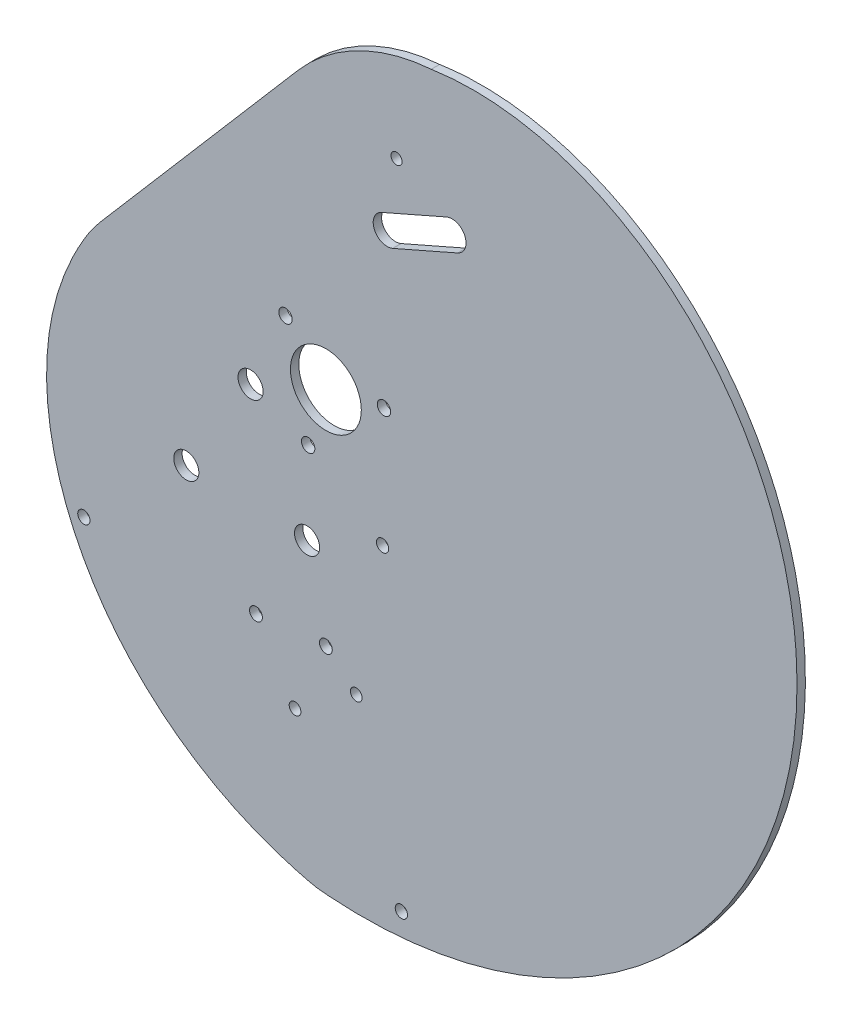
SolidWorks part; units mm, degrees
ref_plane "Front Plane" through (0, 0, 0) normal (0, 0, 1) x (1, 0, 0)
ref_plane "Top Plane" through (0, 0, 0) normal (0, 1, 0) x (1, 0, 0)
ref_plane "Right Plane" through (0, 0, 0) normal (1, 0, 0) x (0, 0, -1)
curve "Curve1"
sketch "Sketch1" plane through (0, 0, 0) normal (0, 0, 1) x (1, 0, 0)
  line L0 (10.9805, 30.1851) -> (22.6104, 35.2876) construction
  line L1 (9.976, 32.4744) -> (21.6059, 37.5769)
  line L2 (11.9849, 27.8957) -> (23.6148, 32.9983)
  line L3 (10.7688, 46.4724) -> (16.7954, 32.7363) construction
  line L4 (-15.5247, -36.542) -> (-17.0714, -47.8252) construction
  line L5 (-12.072, -37.0153) -> (-13.6188, -48.2986) construction
  line L6 (-18.9773, -36.0687) -> (-20.5241, -47.3519) construction
  line L7 (-15.1851, -34.0651) -> (-15.8642, -39.0188) construction
  line L8 (5.6152, 38.2953) -> (3.8561, 42.4197)
  line L9 (20.342, 44.5764) -> (18.4912, 48.9157)
  circle A0 centre (0, 0) radius 6.35
  arc A1 (9.976, 32.4744) -> (11.9849, 27.8957) centre (10.9805, 30.1851) ccw
  arc A2 (23.6148, 32.9983) -> (21.6059, 37.5769) centre (22.6104, 35.2876) ccw
  arc A3 (5.6152, 38.2953) -> (20.342, 44.5764) centre (12.9786, 41.4359) ccw
  arc A4 (-12.072, -37.0153) -> (-18.9773, -36.0687) centre (-15.5247, -36.542) ccw construction
  arc A5 (-20.5241, -47.3519) -> (-13.6188, -48.2986) centre (-17.0714, -47.8252) ccw construction
  spline S0 degree 3 poles (-1.1843, -67.9504) (-0.014, -68.2767) (1.195, -68.3213) (2.3889, -68.4148) (3.5889, -68.4701) (4.791, -68.5105) (5.9959, -68.5295) (7.203, -68.5287) (8.412, -68.5074) (9.6226, -68.4657) (10.8344, -68.4032) (12.047, -68.32) (13.2602, -68.2159) (14.4735, -68.0908) (15.6866, -67.9446) (16.8991, -67.777) (18.1106, -67.5882) (19.3207, -67.3779) (20.529, -67.1461) (21.7351, -66.8927) (22.9386, -66.6176) (24.1392, -66.3208) (25.3362, -66.0022) (26.5295, -65.6619) (27.7184, -65.2996) (28.9026, -64.9155) (30.0816, -64.5096) (31.2551, -64.0817) (32.4225, -63.632) (33.5833, -63.1604) (34.7372, -62.667) (35.8837, -62.1518) (37.0223, -61.6149) (38.1525, -61.0563) (39.2739, -60.4761) (40.3861, -59.8743) (41.4885, -59.2512) (42.5806, -58.6068) (43.6621, -57.9411) (44.7324, -57.2544) (45.791, -56.5468) (46.8375, -55.8184) (47.8714, -55.0695) (48.8923, -54.3001) (49.8996, -53.5105) (50.8929, -52.7009) (51.8717, -51.8715) (52.8356, -51.0225) (53.7841, -50.1542) (54.7166, -49.2668) (55.6329, -48.3607) (56.5323, -47.436) (57.4145, -46.4932) (58.279, -45.5324) (59.1254, -44.554) (59.9531, -43.5583) (60.7619, -42.5458) (61.5512, -41.5167) (62.3207, -40.4714) (63.0698, -39.4103) (63.7983, -38.3338) (64.5057, -37.2423) (65.1916, -36.1362) (65.8556, -35.016) (66.4973, -33.882) (67.1165, -32.7348) (67.7126, -31.5748) (68.2854, -30.4026) (68.8345, -29.2185) (69.3596, -28.023) (69.8603, -26.8168) (70.3364, -25.6003) (70.7876, -24.3741) (71.2134, -23.1386) (71.6138, -21.8945) (71.9884, -20.6423) (72.337, -19.3826) (72.6592, -18.116) (72.955, -16.843) (73.224, -15.5643) (73.4661, -14.2804) (73.6812, -12.992) (73.8689, -11.6997) (74.0292, -10.4042) (74.1619, -9.106) (74.2669, -7.8058) (74.3441, -6.5043) (74.3933, -5.2021) (74.4146, -3.9) (74.4078, -2.5984) (74.3729, -1.2982) (74.3098, -0.0001) (74.2186, 1.2954) (74.0993, 2.5875) (73.9518, 3.8756) (73.7762, 5.1589) (73.5725, 6.4367) (73.3409, 7.7084) (73.0814, 8.9732) (72.7942, 10.2305) (72.4792, 11.4795) (72.1368, 12.7196) (71.767, 13.95) (71.3701, 15.1701) (70.9462, 16.3792) (70.4955, 17.5765) (70.0184, 18.7613) (69.515, 19.9331) (68.9856, 21.091) (68.4305, 22.2344) (67.85, 23.3626) (67.2445, 24.475) (66.6143, 25.5709) (65.9598, 26.6495) (65.2813, 27.7103) (64.5793, 28.7526) (63.8542, 29.7758) (63.1064, 30.7792) (62.3364, 31.7621) (61.5447, 32.7241) (60.7318, 33.6643) (59.8981, 34.5824) (59.0442, 35.4776) (58.1707, 36.3494) (57.2782, 37.1972) (56.3671, 38.0204) (55.4383, 38.8186) (54.4923, 39.5913) (53.53, 40.3381) (52.552, 41.0585) (51.5591, 41.7521) (50.552, 42.4186) (49.5315, 43.0576) (48.4984, 43.6687) (47.4535, 44.2516) (46.3974, 44.8061) (45.3311, 45.3318) (44.2553, 45.8284) (43.1709, 46.2958) (42.0786, 46.7338) (40.9793, 47.1421) (39.8737, 47.5205) (38.7628, 47.869) (37.6473, 48.1874) (36.5281, 48.4755) (35.4061, 48.7334) (34.282, 48.961) (33.1567, 49.1581) (32.031, 49.3249) (30.9059, 49.4613) (29.7821, 49.5673) (28.6604, 49.6431) (27.5418, 49.6886) (26.427, 49.7041) (25.3169, 49.6895) (24.2124, 49.6451) (23.1141, 49.571) (22.0231, 49.4674) (20.94, 49.3346) (19.8657, 49.1727) (18.801, 48.982) (17.7468, 48.7628) (16.7037, 48.5154) (15.6726, 48.2401) (14.6543, 47.9373) (13.6495, 47.6073) (12.659, 47.2504) (11.6836, 46.8672) (10.7239, 46.458) (9.7807, 46.0233) (8.8547, 45.5635) (7.9467, 45.0791) (7.0573, 44.5706) (6.1871, 44.0386) (5.3369, 43.4835) (4.5074, 42.906) (3.699, 42.3065) (2.9126, 41.6858) (2.1491, 41.0448) (1.4087, 40.3857) (0.692, 39.711) (-0.0007, 39.0233) (-0.6692, 38.3252) (-1.3135, 37.6192) (-1.9336, 36.908) (-2.5298, 36.194) (-3.1024, 35.4799) (-3.6521, 34.7682) (-4.1795, 34.0612) (-4.6854, 33.3616) (-5.1709, 32.6716) (-5.637, 31.9937) (-6.085, 31.3301) (-6.5163, 30.6831) (-6.9325, 30.0548) (-7.3352, 29.4474) (-7.7263, 28.8629) (-8.1078, 28.3032) (-8.4816, 27.77) (-8.8501, 27.2652) (-9.216, 26.7897) (-9.5801, 26.3424) (-9.9432, 25.9213) (-10.3062, 25.5243) (-10.6698, 25.1494) (-11.0346, 24.7946) (-11.4009, 24.4578) (-11.7691, 24.1369) (-12.1394, 23.8299) (-12.5117, 23.5348) (-12.8861, 23.2497) (-13.2622, 22.9725) (-13.6397, 22.7014) (-14.0182, 22.4345) (-14.3971, 22.1699) (-14.7757, 21.906) (-15.1531, 21.6409) (-15.5285, 21.3732) (-15.9009, 21.1012) (-16.269, 20.8234) (-16.6317, 20.5384) (-16.9875, 20.2449) (-17.3351, 19.9417) (-17.6745, 19.6295) (-18.0059, 19.3089) (-18.3295, 18.9807) (-18.6455, 18.6455) (-18.9542, 18.3039) (-19.2559, 17.9565) (-19.5509, 17.6038) (-19.8396, 17.2464) (-20.1224, 16.8848) (-20.3997, 16.5195) (-20.672, 16.1508) (-20.9397, 15.7793) (-21.2033, 15.4052) (-21.4634, 15.0289) (-21.7205, 14.6507) (-21.9753, 14.2708) (-22.2281, 13.8895) (-22.4798, 13.507) (-22.7308, 13.1233) (-22.9819, 12.7386) (-23.2336, 12.3529) (-23.4866, 11.9663) (-23.7416, 11.5787) (-23.9993, 11.19) (-24.2602, 10.8001) (-24.5251, 10.4088) (-24.7947, 10.016) (-25.0696, 9.6214) (-25.3504, 9.2246) (-25.6379, 8.8254) (-25.9327, 8.4234) (-26.2354, 8.018) (-26.5467, 7.609) (-26.8672, 7.1956) (-27.1974, 6.7776) (-27.537, 6.3539) (-27.8856, 5.9238) (-28.2424, 5.4864) (-28.6069, 5.0408) (-28.9783, 4.5865) (-29.3562, 4.1226) (-29.7396, 3.6485) (-30.1278, 3.1637) (-30.5202, 2.6674) (-30.9158, 2.1592) (-31.314, 1.6386) (-31.7137, 1.1051) (-32.1143, 0.5583) (-32.5148, -0.0021) (-32.9143, -0.5765) (-33.3119, -1.1651) (-33.7067, -1.7682) (-34.0978, -2.3859) (-34.4843, -3.0184) (-34.8652, -3.6658) (-35.2396, -4.3281) (-35.6066, -5.0053) (-35.9651, -5.6973) (-36.3143, -6.404) (-36.6531, -7.1254) (-36.9808, -7.8611) (-37.2963, -8.611) (-37.5988, -9.3748) (-37.8873, -10.1521) (-38.1609, -10.9426) (-38.4187, -11.7459) (-38.66, -12.5613) (-38.8837, -13.3886) (-39.0892, -14.2271) (-39.2755, -15.0762) (-39.4422, -15.9354) (-39.589, -16.8043) (-39.7155, -17.6823) (-39.8215, -18.5689) (-39.9067, -19.4636) (-39.9709, -20.366) (-40.0137, -21.2755) (-40.035, -22.1916) (-40.0345, -23.1138) (-40.0119, -24.0415) (-39.9672, -24.9742) (-39.9002, -25.9114) (-39.8105, -26.8525) (-39.6982, -27.7969) (-39.563, -28.7442) (-39.4048, -29.6936) (-39.2235, -30.6448) (-39.019, -31.597) (-38.7911, -32.5497) (-38.5399, -33.5023) (-38.2653, -34.4543) (-37.9672, -35.4051) (-37.6456, -36.354) (-37.3004, -37.3005) (-36.9317, -38.2441) (-36.5395, -39.184) (-36.1238, -40.1197) (-35.6847, -41.0507) (-35.2221, -41.9763) (-34.7363, -42.896) (-34.2272, -43.8091) (-33.695, -44.715) (-33.1398, -45.6133) (-32.5617, -46.5032) (-31.9609, -47.3843) (-31.3375, -48.2559) (-30.6917, -49.1174) (-30.0238, -49.9683) (-29.3338, -50.808) (-28.6221, -51.636) (-27.8888, -52.4517) (-27.1343, -53.2545) (-26.3587, -54.0439) (-25.5624, -54.8193) (-24.7457, -55.5802) (-23.9088, -56.3261) (-23.0521, -57.0564) (-22.1759, -57.7707) (-21.2805, -58.4684) (-20.3664, -59.149) (-19.4339, -59.812) (-18.4833, -60.4569) (-17.5151, -61.0833) (-16.5298, -61.6908) (-15.5276, -62.2787) (-14.5091, -62.8467) (-13.4747, -63.3944) (-12.4248, -63.9213) (-11.36, -64.4271) (-10.2807, -64.9112) (-9.1874, -65.3733) (-8.0806, -65.8131) (-6.9608, -66.2301) (-5.8286, -66.6239) (-4.6845, -66.9947) (-3.5289, -67.3403) (-2.3631, -67.6669) (-1.1843, -67.9504) (-0.014, -68.2767) (1.195, -68.3213) knots -0.0101 -0.006743 -0.003377 0 0.00332 0.006645 0.009976 0.013312 0.016655 0.020003 0.023357 0.026716 0.030082 0.033453 0.036831 0.040214 0.043603 0.046998 0.050399 0.053806 0.057218 0.060637 0.064061 0.067491 0.070927 0.074369 0.077816 0.081269 0.084728 0.088192 0.091662 0.095138 0.098619 0.102105 0.105597 0.109094 0.112596 0.116103 0.119615 0.123133 0.126655 0.130182 0.133714 0.137251 0.140792 0.144337 0.147888 0.151442 0.155 0.158563 0.16213 0.1657 0.169275 0.172853 0.176434 0.180019 0.183607 0.187199 0.190793 0.19439 0.19799 0.201593 0.205199 0.208806 0.212416 0.216028 0.219642 0.223258 0.226875 0.230494 0.234115 0.237736 0.241359 0.244982 0.248606 0.252231 0.255856 0.259481 0.263106 0.266731 0.270356 0.273981 0.277605 0.281228 0.28485 0.28847 0.29209 0.295708 0.299324 0.302939 0.306551 0.310161 0.313769 0.317374 0.320976 0.324575 0.328171 0.331763 0.335352 0.338938 0.342519 0.346096 0.349669 0.353237 0.356801 0.360359 0.363913 0.367461 0.371004 0.374541 0.378073 0.381598 0.385117 0.38863 0.392136 0.395636 0.399128 0.402614 0.406092 0.409563 0.413026 0.416482 0.419929 0.423369 0.4268 0.430223 0.433637 0.437043 0.44044 0.443828 0.447206 0.450575 0.453935 0.457284 0.460624 0.463953 0.467272 0.47058 0.473877 0.477164 0.480439 0.483703 0.486955 0.490196 0.493426 0.496643 0.499848 0.503042 0.506223 0.509391 0.512547 0.515691 0.518822 0.52194 0.525045 0.528137 0.531216 0.534282 0.537335 0.540375 0.543401 0.546414 0.549414 0.5524 0.555374 0.558333 0.56128 0.564213 0.567133 0.57004 0.572933 0.575814 0.578681 0.581535 0.584377 0.587205 0.590021 0.592825 0.595616 0.598394 0.60116 0.603911 0.606642 0.60935 0.612032 0.614684 0.617303 0.619884 0.622424 0.62492 0.627367 0.629763 0.632104 0.634387 0.636609 0.638767 0.640858 0.64288 0.644831 0.64671 0.648517 0.65025 0.651911 0.653509 0.655048 0.656538 0.657984 0.659394 0.660772 0.662125 0.663458 0.664774 0.666078 0.667373 0.668662 0.669946 0.671227 0.672507 0.673786 0.675065 0.676344 0.677623 0.678903 0.680182 0.681461 0.68274 0.684019 0.685298 0.686575 0.687853 0.689129 0.690404 0.691679 0.692952 0.694224 0.695495 0.696765 0.698035 0.699304 0.700572 0.70184 0.703109 0.704379 0.705651 0.706925 0.708202 0.709483 0.71077 0.712063 0.713364 0.714674 0.715995 0.717328 0.718676 0.72004 0.721422 0.722825 0.72425 0.7257 0.727177 0.728683 0.730218 0.731784 0.73338 0.735008 0.736668 0.738359 0.740082 0.741837 0.743623 0.745441 0.747291 0.749171 0.751082 0.753022 0.754993 0.756992 0.759021 0.761077 0.76316 0.765271 0.767407 0.769569 0.771756 0.773967 0.776201 0.778458 0.780736 0.783036 0.785357 0.787697 0.790056 0.792433 0.794828 0.797239 0.799666 0.80211 0.804571 0.807047 0.80954 0.812049 0.814575 0.817116 0.819674 0.822248 0.824838 0.827444 0.830066 0.832704 0.835358 0.838027 0.840713 0.843414 0.846131 0.848864 0.851612 0.854376 0.857155 0.859949 0.862759 0.865584 0.868424 0.871279 0.874149 0.877033 0.879933 0.882847 0.885776 0.88872 0.891678 0.89465 0.897636 0.900637 0.903651 0.906679 0.909721 0.912777 0.915847 0.91893 0.922026 0.925135 0.928258 0.931393 0.934541 0.937702 0.940876 0.944062 0.947261 0.950471 0.953694 0.956929 0.960175 0.963433 0.966703 0.969984 0.973276 0.976579 0.979893 0.983218 0.986554 0.9899 0.993257 0.996623 1 1.00332 1.006645 1.009976 only from (0, -68.2309) to (0, -68.2309) construction
  spline S1 degree 3 poles (-1.1843, -67.9504) (-0.014, -68.2767) (1.195, -68.3213) (2.3889, -68.4148) (3.5889, -68.4701) (4.791, -68.5105) (5.9959, -68.5295) (7.203, -68.5287) (8.412, -68.5074) (9.6226, -68.4657) (10.8344, -68.4032) (12.047, -68.32) (13.2602, -68.2159) (14.4735, -68.0908) (15.6866, -67.9446) (16.8991, -67.777) (18.1106, -67.5882) (19.3207, -67.3779) (20.529, -67.1461) (21.7351, -66.8927) (22.9386, -66.6176) (24.1392, -66.3208) (25.3362, -66.0022) (26.5295, -65.6619) (27.7184, -65.2996) (28.9026, -64.9155) (30.0816, -64.5096) (31.2551, -64.0817) (32.4225, -63.632) (33.5833, -63.1604) (34.7372, -62.667) (35.8837, -62.1518) (37.0223, -61.6149) (38.1525, -61.0563) (39.2739, -60.4761) (40.3861, -59.8743) (41.4885, -59.2512) (42.5806, -58.6068) (43.6621, -57.9411) (44.7324, -57.2544) (45.791, -56.5468) (46.8375, -55.8184) (47.8714, -55.0695) (48.8923, -54.3001) (49.8996, -53.5105) (50.8929, -52.7009) (51.8717, -51.8715) (52.8356, -51.0225) (53.7841, -50.1542) (54.7166, -49.2668) (55.6329, -48.3607) (56.5323, -47.436) (57.4145, -46.4932) (58.279, -45.5324) (59.1254, -44.554) (59.9531, -43.5583) (60.7619, -42.5458) (61.5512, -41.5167) (62.3207, -40.4714) (63.0698, -39.4103) (63.7983, -38.3338) (64.5057, -37.2423) (65.1916, -36.1362) (65.8556, -35.016) (66.4973, -33.882) (67.1165, -32.7348) (67.7126, -31.5748) (68.2854, -30.4026) (68.8345, -29.2185) (69.3596, -28.023) (69.8603, -26.8168) (70.3364, -25.6003) (70.7876, -24.3741) (71.2134, -23.1386) (71.6138, -21.8945) (71.9884, -20.6423) (72.337, -19.3826) (72.6592, -18.116) (72.955, -16.843) (73.224, -15.5643) (73.4661, -14.2804) (73.6812, -12.992) (73.8689, -11.6997) (74.0292, -10.4042) (74.1619, -9.106) (74.2669, -7.8058) (74.3441, -6.5043) (74.3933, -5.2021) (74.4146, -3.9) (74.4078, -2.5984) (74.3729, -1.2982) (74.3098, -0.0001) (74.2186, 1.2954) (74.0993, 2.5875) (73.9518, 3.8756) (73.7762, 5.1589) (73.5725, 6.4367) (73.3409, 7.7084) (73.0814, 8.9732) (72.7942, 10.2305) (72.4792, 11.4795) (72.1368, 12.7196) (71.767, 13.95) (71.3701, 15.1701) (70.9462, 16.3792) (70.4955, 17.5765) (70.0184, 18.7613) (69.515, 19.9331) (68.9856, 21.091) (68.4305, 22.2344) (67.85, 23.3626) (67.2445, 24.475) (66.6143, 25.5709) (65.9598, 26.6495) (65.2813, 27.7103) (64.5793, 28.7526) (63.8542, 29.7758) (63.1064, 30.7792) (62.3364, 31.7621) (61.5447, 32.7241) (60.7318, 33.6643) (59.8981, 34.5824) (59.0442, 35.4776) (58.1707, 36.3494) (57.2782, 37.1972) (56.3671, 38.0204) (55.4383, 38.8186) (54.4923, 39.5913) (53.53, 40.3381) (52.552, 41.0585) (51.5591, 41.7521) (50.552, 42.4186) (49.5315, 43.0576) (48.4984, 43.6687) (47.4535, 44.2516) (46.3974, 44.8061) (45.3311, 45.3318) (44.2553, 45.8284) (43.1709, 46.2958) (42.0786, 46.7338) (40.9793, 47.1421) (39.8737, 47.5205) (38.7628, 47.869) (37.6473, 48.1874) (36.5281, 48.4755) (35.4061, 48.7334) (34.282, 48.961) (33.1567, 49.1581) (32.031, 49.3249) (30.9059, 49.4613) (29.7821, 49.5673) (28.6604, 49.6431) (27.5418, 49.6886) (26.427, 49.7041) (25.3169, 49.6895) (24.2124, 49.6451) (23.1141, 49.571) (22.0231, 49.4674) (20.94, 49.3346) (19.8657, 49.1727) (18.801, 48.982) (17.7468, 48.7628) (16.7037, 48.5154) (15.6726, 48.2401) (14.6543, 47.9373) (13.6495, 47.6073) (12.659, 47.2504) (11.6836, 46.8672) (10.7239, 46.458) (9.7807, 46.0233) (8.8547, 45.5635) (7.9467, 45.0791) (7.0573, 44.5706) (6.1871, 44.0386) (5.3369, 43.4835) (4.5074, 42.906) (3.699, 42.3065) (2.9126, 41.6858) (2.1491, 41.0448) (1.4087, 40.3857) (0.692, 39.711) (-0.0007, 39.0233) (-0.6692, 38.3252) (-1.3135, 37.6192) (-1.9336, 36.908) (-2.5298, 36.194) (-3.1024, 35.4799) (-3.6521, 34.7682) (-4.1795, 34.0612) (-4.6854, 33.3616) (-5.1709, 32.6716) (-5.637, 31.9937) (-6.085, 31.3301) (-6.5163, 30.6831) (-6.9325, 30.0548) (-7.3352, 29.4474) (-7.7263, 28.8629) (-8.1078, 28.3032) (-8.4816, 27.77) (-8.8501, 27.2652) (-9.216, 26.7897) (-9.5801, 26.3424) (-9.9432, 25.9213) (-10.3062, 25.5243) (-10.6698, 25.1494) (-11.0346, 24.7946) (-11.4009, 24.4578) (-11.7691, 24.1369) (-12.1394, 23.8299) (-12.5117, 23.5348) (-12.8861, 23.2497) (-13.2622, 22.9725) (-13.6397, 22.7014) (-14.0182, 22.4345) (-14.3971, 22.1699) (-14.7757, 21.906) (-15.1531, 21.6409) (-15.5285, 21.3732) (-15.9009, 21.1012) (-16.269, 20.8234) (-16.6317, 20.5384) (-16.9875, 20.2449) (-17.3351, 19.9417) (-17.6745, 19.6295) (-18.0059, 19.3089) (-18.3295, 18.9807) (-18.6455, 18.6455) (-18.9542, 18.3039) (-19.2559, 17.9565) (-19.5509, 17.6038) (-19.8396, 17.2464) (-20.1224, 16.8848) (-20.3997, 16.5195) (-20.672, 16.1508) (-20.9397, 15.7793) (-21.2033, 15.4052) (-21.4634, 15.0289) (-21.7205, 14.6507) (-21.9753, 14.2708) (-22.2281, 13.8895) (-22.4798, 13.507) (-22.7308, 13.1233) (-22.9819, 12.7386) (-23.2336, 12.3529) (-23.4866, 11.9663) (-23.7416, 11.5787) (-23.9993, 11.19) (-24.2602, 10.8001) (-24.5251, 10.4088) (-24.7947, 10.016) (-25.0696, 9.6214) (-25.3504, 9.2246) (-25.6379, 8.8254) (-25.9327, 8.4234) (-26.2354, 8.018) (-26.5467, 7.609) (-26.8672, 7.1956) (-27.1974, 6.7776) (-27.537, 6.3539) (-27.8856, 5.9238) (-28.2424, 5.4864) (-28.6069, 5.0408) (-28.9783, 4.5865) (-29.3562, 4.1226) (-29.7396, 3.6485) (-30.1278, 3.1637) (-30.5202, 2.6674) (-30.9158, 2.1592) (-31.314, 1.6386) (-31.7137, 1.1051) (-32.1143, 0.5583) (-32.5148, -0.0021) (-32.9143, -0.5765) (-33.3119, -1.1651) (-33.7067, -1.7682) (-34.0978, -2.3859) (-34.4843, -3.0184) (-34.8652, -3.6658) (-35.2396, -4.3281) (-35.6066, -5.0053) (-35.9651, -5.6973) (-36.3143, -6.404) (-36.6531, -7.1254) (-36.9808, -7.8611) (-37.2963, -8.611) (-37.5988, -9.3748) (-37.8873, -10.1521) (-38.1609, -10.9426) (-38.4187, -11.7459) (-38.66, -12.5613) (-38.8837, -13.3886) (-39.0892, -14.2271) (-39.2755, -15.0762) (-39.4422, -15.9354) (-39.589, -16.8043) (-39.7155, -17.6823) (-39.8215, -18.5689) (-39.9067, -19.4636) (-39.9709, -20.366) (-40.0137, -21.2755) (-40.035, -22.1916) (-40.0345, -23.1138) (-40.0119, -24.0415) (-39.9672, -24.9742) (-39.9002, -25.9114) (-39.8105, -26.8525) (-39.6982, -27.7969) (-39.563, -28.7442) (-39.4048, -29.6936) (-39.2235, -30.6448) (-39.019, -31.597) (-38.7911, -32.5497) (-38.5399, -33.5023) (-38.2653, -34.4543) (-37.9672, -35.4051) (-37.6456, -36.354) (-37.3004, -37.3005) (-36.9317, -38.2441) (-36.5395, -39.184) (-36.1238, -40.1197) (-35.6847, -41.0507) (-35.2221, -41.9763) (-34.7363, -42.896) (-34.2272, -43.8091) (-33.695, -44.715) (-33.1398, -45.6133) (-32.5617, -46.5032) (-31.9609, -47.3843) (-31.3375, -48.2559) (-30.6917, -49.1174) (-30.0238, -49.9683) (-29.3338, -50.808) (-28.6221, -51.636) (-27.8888, -52.4517) (-27.1343, -53.2545) (-26.3587, -54.0439) (-25.5624, -54.8193) (-24.7457, -55.5802) (-23.9088, -56.3261) (-23.0521, -57.0564) (-22.1759, -57.7707) (-21.2805, -58.4684) (-20.3664, -59.149) (-19.4339, -59.812) (-18.4833, -60.4569) (-17.5151, -61.0833) (-16.5298, -61.6908) (-15.5276, -62.2787) (-14.5091, -62.8467) (-13.4747, -63.3944) (-12.4248, -63.9213) (-11.36, -64.4271) (-10.2807, -64.9112) (-9.1874, -65.3733) (-8.0806, -65.8131) (-6.9608, -66.2301) (-5.8286, -66.6239) (-4.6845, -66.9947) (-3.5289, -67.3403) (-2.3631, -67.6669) (-1.1843, -67.9504) (-0.014, -68.2767) (1.195, -68.3213) knots -0.0101 -0.006743 -0.003377 0 0.00332 0.006645 0.009976 0.013312 0.016655 0.020003 0.023357 0.026716 0.030082 0.033453 0.036831 0.040214 0.043603 0.046998 0.050399 0.053806 0.057218 0.060637 0.064061 0.067491 0.070927 0.074369 0.077816 0.081269 0.084728 0.088192 0.091662 0.095138 0.098619 0.102105 0.105597 0.109094 0.112596 0.116103 0.119615 0.123133 0.126655 0.130182 0.133714 0.137251 0.140792 0.144337 0.147888 0.151442 0.155 0.158563 0.16213 0.1657 0.169275 0.172853 0.176434 0.180019 0.183607 0.187199 0.190793 0.19439 0.19799 0.201593 0.205199 0.208806 0.212416 0.216028 0.219642 0.223258 0.226875 0.230494 0.234115 0.237736 0.241359 0.244982 0.248606 0.252231 0.255856 0.259481 0.263106 0.266731 0.270356 0.273981 0.277605 0.281228 0.28485 0.28847 0.29209 0.295708 0.299324 0.302939 0.306551 0.310161 0.313769 0.317374 0.320976 0.324575 0.328171 0.331763 0.335352 0.338938 0.342519 0.346096 0.349669 0.353237 0.356801 0.360359 0.363913 0.367461 0.371004 0.374541 0.378073 0.381598 0.385117 0.38863 0.392136 0.395636 0.399128 0.402614 0.406092 0.409563 0.413026 0.416482 0.419929 0.423369 0.4268 0.430223 0.433637 0.437043 0.44044 0.443828 0.447206 0.450575 0.453935 0.457284 0.460624 0.463953 0.467272 0.47058 0.473877 0.477164 0.480439 0.483703 0.486955 0.490196 0.493426 0.496643 0.499848 0.503042 0.506223 0.509391 0.512547 0.515691 0.518822 0.52194 0.525045 0.528137 0.531216 0.534282 0.537335 0.540375 0.543401 0.546414 0.549414 0.5524 0.555374 0.558333 0.56128 0.564213 0.567133 0.57004 0.572933 0.575814 0.578681 0.581535 0.584377 0.587205 0.590021 0.592825 0.595616 0.598394 0.60116 0.603911 0.606642 0.60935 0.612032 0.614684 0.617303 0.619884 0.622424 0.62492 0.627367 0.629763 0.632104 0.634387 0.636609 0.638767 0.640858 0.64288 0.644831 0.64671 0.648517 0.65025 0.651911 0.653509 0.655048 0.656538 0.657984 0.659394 0.660772 0.662125 0.663458 0.664774 0.666078 0.667373 0.668662 0.669946 0.671227 0.672507 0.673786 0.675065 0.676344 0.677623 0.678903 0.680182 0.681461 0.68274 0.684019 0.685298 0.686575 0.687853 0.689129 0.690404 0.691679 0.692952 0.694224 0.695495 0.696765 0.698035 0.699304 0.700572 0.70184 0.703109 0.704379 0.705651 0.706925 0.708202 0.709483 0.71077 0.712063 0.713364 0.714674 0.715995 0.717328 0.718676 0.72004 0.721422 0.722825 0.72425 0.7257 0.727177 0.728683 0.730218 0.731784 0.73338 0.735008 0.736668 0.738359 0.740082 0.741837 0.743623 0.745441 0.747291 0.749171 0.751082 0.753022 0.754993 0.756992 0.759021 0.761077 0.76316 0.765271 0.767407 0.769569 0.771756 0.773967 0.776201 0.778458 0.780736 0.783036 0.785357 0.787697 0.790056 0.792433 0.794828 0.797239 0.799666 0.80211 0.804571 0.807047 0.80954 0.812049 0.814575 0.817116 0.819674 0.822248 0.824838 0.827444 0.830066 0.832704 0.835358 0.838027 0.840713 0.843414 0.846131 0.848864 0.851612 0.854376 0.857155 0.859949 0.862759 0.865584 0.868424 0.871279 0.874149 0.877033 0.879933 0.882847 0.885776 0.88872 0.891678 0.89465 0.897636 0.900637 0.903651 0.906679 0.909721 0.912777 0.915847 0.91893 0.922026 0.925135 0.928258 0.931393 0.934541 0.937702 0.940876 0.944062 0.947261 0.950471 0.953694 0.956929 0.960175 0.963433 0.966703 0.969984 0.973276 0.976579 0.979893 0.983218 0.986554 0.9899 0.993257 0.996623 1 1.00332 1.006645 1.009976 only from (0, -68.2309) to (0, -68.2309)
  point P6 (16.7954, 32.7363)
  point P18 (-16.298, -42.1836)
  dimension "D1" = 12.7
  dimension "D5" = 5.5
  dimension "D2" = 12.7
  dimension "D3" = 5
  dimension "D4" = 15
extrude "Boss-Extrude1" add sketch "Sketch1" along normal mid plane 1.5 contours A3 S1 A0 A2 L2 A1 L1
sketch "Sketch2" plane through (0, 0, 0) normal (0, 0, 1) x (1, 0, 0)
  line L0 (4.6222, 43.3119) -> (-35.7001, -3.6508) construction
  line L1 (-35.7001, -3.6508) -> (-7.0727, 43.3119)
  line L2 (-7.0727, 43.3119) -> (4.6222, 43.3119)
  line L3 (7.6571, 40.7062) -> (-41.2002, -16.1969)
  line L4 (4.6222, 43.3119) -> (7.6571, 40.7062)
  line L5 (-35.7001, -3.6508) -> (-41.2002, -16.1969)
extrude "Cut-Extrude1" cut sketch "Sketch2" against normal through all both and the other way through all
fillet "Fillet1" radius 20 1 edges at (-38.9189, -13.5399, 0)
sketch "Sketch3" plane through (0, 0, 0.75) normal (0, 0, 1) x (1, 0, 0)
  point P0 (-13.488, -5.936)
  point P1 (-3.3675, -25.0764)
  point P3 (-25.0038, -24.2708)
fillet "Fillet2" [suppressed] radius 2.5
fillet "Fillet3" [suppressed] radius 1
sketch "Sketch6" plane through (0, 0, 0) normal (0, 0, 1) x (1, 0, 0)
  line L2 (-40.2409, 5.985) -> (-5.0109, 47.0167)
  line L3 (-40.2409, 5.985) -> (-5.0109, 47.0167)
  arc A1 (-5.0109, 47.0167) -> (18.8738, 59.1348) centre (21.5961, 24.1717) cw
  arc A2 (-40.2409, 5.985) -> (-43.3928, 1.5586) centre (-17.4796, -13.5579) ccw
  arc A3 (-40.2409, 5.985) -> (-43.3928, 1.5586) centre (-17.4796, -13.5579) ccw
  spline S2 degree 3 poles (28661.4102, -17966.147) (-737.5513, -1850.2813) (-229.9648, 76.7678) (33.4507, 59.3461) (37.0313, 58.7272) (43.9674, 56.8115) (47.3229, 55.515) (53.7078, 52.3312) (56.7371, 50.4441) (62.3895, 46.1692) (65.0134, 43.7791) (69.7846, 38.6064) (71.9342, 35.8236) (75.7327, 29.9643) (77.3816, 26.8878) (80.1644, 20.5326) (81.2983, 17.2539) (83.0485, 10.579) (83.6648, 7.183) (84.3866, 0.3517) (84.4921, -3.0835) (84.2072, -9.921) (83.8168, -13.3233) (82.562, -20.0286) (81.6977, -23.3317) (78.4358, -33.0013) (75.367, -39.1258) (67.7295, -50.3171) (63.1613, -55.384) (52.8841, -64.1458) (47.1758, -67.8403) (35.0265, -73.6501) (28.5867, -75.7651) (18.7016, -77.6861) (15.3691, -78.1188) (10.3543, -78.4567) (8.6797, -78.5176) (6.5875, -78.5294) (6.1701, -78.5285) (5.3343, -78.5205) (4.9137, -78.5133) (4.072, -78.492) (3.6586, -78.4781) (3.0497, -78.4542) (2.8432, -78.4455) (2.4135, -78.4255) (2.1919, -78.4141) (1.8492, -78.3942) (1.7308, -78.3869) (1.5098, -78.3725) (1.4058, -78.3654) (1.1132, -78.3453) (0.944, -78.3334) (0.7644, -78.3218) (0.7301, -78.3196) (0.6646, -78.3156) (0.6353, -78.3139) (0.5391, -78.3084) (0.4507, -78.3038) (0.1135, -78.285) (-0.2076, -78.2671) (-0.8333, -78.2062) (-1.0659, -78.1799) (-1.4499, -78.1259) (-1.5869, -78.1048) (-1.8434, -78.0619) (-1.9656, -78.0398) (-2.5465, -77.9285) (-2.9147, -77.8384) (-3.3304, -77.7331) (-3.4462, -77.7027) (-3.5862, -77.666) (-3.6273, -77.6553) (-3.6982, -77.6367) (-3.7277, -77.6291) (-3.8942, -77.5863) (-4.2091, -77.5075) (-4.6212, -77.4044) (-4.966, -77.3149) (-5.0818, -77.2843) (-5.3074, -77.2239) (-5.6407, -77.1332) (-5.9586, -77.0433) (-6.369, -76.9253) (-6.5693, -76.8669) (-7.1822, -76.6851) (-7.5996, -76.5573) (-8.4299, -76.2933) (-8.8413, -76.1578) (-10.8906, -75.4606) (-12.5146, -74.8354) (-15.706, -73.4558) (-17.2758, -72.7006) (-21.8904, -70.2423) (-24.8406, -68.3459) (-30.3947, -64.0648) (-32.9986, -61.6801) (-37.7616, -56.4643) (-39.9206, -53.6333) (-43.6909, -47.5866) (-45.3021, -44.3706) (-47.8702, -37.6402) (-48.8271, -34.1252) (-49.9786, -26.9144) (-50.173, -23.218) (-49.8137, -17.6585) (-49.5855, -15.8032) (-49.0714, -13.0362) (-48.8708, -12.115) (-48.4149, -10.2934) (-48.1596, -9.3921) (-47.3164, -6.7212) (-46.6509, -4.9846) (39.9764, 188.1749) (1275.4095, -345.1148) (-28879.2526, -17933.6776) knots -2.206128 -2.206128 -2.206128 -2.206128 0.03125 0.03125 0.0625 0.0625 0.09375 0.09375 0.125 0.125 0.15625 0.15625 0.1875 0.1875 0.21875 0.21875 0.25 0.25 0.28125 0.28125 0.3125 0.3125 0.34375 0.34375 0.375 0.375 0.4375 0.4375 0.5 0.5 0.5625 0.5625 0.625 0.625 0.65625 0.65625 0.671875 0.671875 0.675781 0.675781 0.679687 0.679687 0.683594 0.683594 0.685547 0.685547 0.6875 0.6875 0.688477 0.688477 0.689453 0.689453 0.691406 0.691406 0.691895 0.691895 0.692383 0.692383 0.693359 0.693359 0.695312 0.695312 0.696289 0.696289 0.696777 0.696777 0.697266 0.697266 0.699219 0.699219 0.700195 0.700195 0.700684 0.700684 0.701172 0.701172 0.703125 0.705078 0.705078 0.706055 0.706055 0.707031 0.708984 0.708984 0.710937 0.710937 0.714844 0.714844 0.71875 0.71875 0.734375 0.734375 0.75 0.75 0.78125 0.78125 0.8125 0.8125 0.84375 0.84375 0.875 0.875 0.90625 0.90625 0.9375 0.9375 0.953125 0.953125 0.960937 0.960937 0.96875 0.96875 0.984375 0.984375 2.764789 2.764789 2.764789 2.764789 only from (18.8738, 59.1348) to (-43.3928, 1.5586)
  spline S3 degree 3 poles (18.8738, 59.1348) (22.5168, 59.6868) (26.1937, 59.8261) (33.4507, 59.3461) (37.0313, 58.7272) (43.9674, 56.8115) (47.3229, 55.515) (53.7078, 52.3312) (56.7371, 50.4441) (62.3895, 46.1692) (65.0134, 43.7791) (69.7846, 38.6064) (71.9342, 35.8236) (75.7327, 29.9643) (77.3816, 26.8878) (80.1644, 20.5326) (81.2983, 17.2539) (83.0485, 10.579) (83.6648, 7.183) (84.3866, 0.3517) (84.4921, -3.0835) (84.2072, -9.921) (83.8168, -13.3233) (82.562, -20.0286) (81.6977, -23.3317) (78.4358, -33.0013) (75.367, -39.1258) (67.7295, -50.3171) (63.1613, -55.384) (52.8841, -64.1458) (47.1758, -67.8403) (35.0265, -73.6501) (28.5867, -75.7651) (18.7016, -77.6861) (15.3691, -78.1188) (10.3543, -78.4567) (8.6797, -78.5176) (6.5875, -78.5294) (6.1701, -78.5285) (5.3343, -78.5205) (4.9137, -78.5133) (4.072, -78.492) (3.6586, -78.4781) (3.0497, -78.4542) (2.8432, -78.4455) (2.4135, -78.4255) (2.1919, -78.4141) (1.8492, -78.3942) (1.7308, -78.3869) (1.5098, -78.3725) (1.4058, -78.3654) (1.1132, -78.3453) (0.944, -78.3334) (0.7644, -78.3218) (0.7301, -78.3196) (0.6646, -78.3156) (0.6353, -78.3139) (0.5391, -78.3084) (0.4507, -78.3038) (0.1135, -78.285) (-0.2076, -78.2671) (-0.8333, -78.2062) (-1.0659, -78.1799) (-1.4499, -78.1259) (-1.5869, -78.1048) (-1.8434, -78.0619) (-1.9656, -78.0398) (-2.5465, -77.9285) (-2.9147, -77.8384) (-3.3304, -77.7331) (-3.4462, -77.7027) (-3.5862, -77.666) (-3.6273, -77.6553) (-3.6982, -77.6367) (-3.7277, -77.6291) (-3.8942, -77.5863) (-4.2091, -77.5075) (-4.6212, -77.4044) (-4.966, -77.3149) (-5.0818, -77.2843) (-5.3074, -77.2239) (-5.6407, -77.1332) (-5.9586, -77.0433) (-6.369, -76.9253) (-6.5693, -76.8669) (-7.1822, -76.6851) (-7.5996, -76.5573) (-8.4299, -76.2933) (-8.8413, -76.1578) (-10.8906, -75.4606) (-12.5146, -74.8354) (-15.706, -73.4558) (-17.2758, -72.7006) (-21.8904, -70.2423) (-24.8406, -68.3459) (-30.3947, -64.0648) (-32.9986, -61.6801) (-37.7616, -56.4643) (-39.9206, -53.6333) (-43.6909, -47.5866) (-45.3021, -44.3706) (-47.8702, -37.6402) (-48.8271, -34.1252) (-49.9786, -26.9144) (-50.173, -23.218) (-49.8137, -17.6585) (-49.5855, -15.8032) (-49.0714, -13.0362) (-48.8708, -12.115) (-48.4149, -10.2934) (-48.1596, -9.3921) (-47.3164, -6.7212) (-46.6509, -4.9846) (-45.1437, -1.6238) (-44.3015, 0.0008) (-43.3928, 1.5586) knots 0 0 0 0 0.03125 0.03125 0.0625 0.0625 0.09375 0.09375 0.125 0.125 0.15625 0.15625 0.1875 0.1875 0.21875 0.21875 0.25 0.25 0.28125 0.28125 0.3125 0.3125 0.34375 0.34375 0.375 0.375 0.4375 0.4375 0.5 0.5 0.5625 0.5625 0.625 0.625 0.65625 0.65625 0.671875 0.671875 0.675781 0.675781 0.679687 0.679687 0.683594 0.683594 0.685547 0.685547 0.6875 0.6875 0.688477 0.688477 0.689453 0.689453 0.691406 0.691406 0.691895 0.691895 0.692383 0.692383 0.693359 0.693359 0.695312 0.695312 0.696289 0.696289 0.696777 0.696777 0.697266 0.697266 0.699219 0.699219 0.700195 0.700195 0.700684 0.700684 0.701172 0.701172 0.703125 0.705078 0.705078 0.706055 0.706055 0.707031 0.708984 0.708984 0.710937 0.710937 0.714844 0.714844 0.71875 0.71875 0.734375 0.734375 0.75 0.75 0.78125 0.78125 0.8125 0.8125 0.84375 0.84375 0.875 0.875 0.90625 0.90625 0.9375 0.9375 0.953125 0.953125 0.960937 0.960937 0.96875 0.96875 0.984375 0.984375 1 1 1 1
  dimension "D1" = 10
extrude "Boss-Extrude2" add sketch "Sketch6" along normal mid plane 1.5
sketch "Sketch7" plane through (0, 0, 0) normal (0, 0, 1) x (1, 0, 0)
  circle A0 centre (0, 0) radius 6.35
  circle A1 centre (0, 0) radius 3.175
  dimension "D1" = 6.35
extrude "Boss-Extrude3" add sketch "Sketch7" along normal mid plane 1.5
sketch "Sketch8" plane through (0, 0, 0) normal (0, 0, 1) x (1, 0, 0)
  line L0 (10.9805, 30.1851) -> (22.6104, 35.2876) construction
  line L1 (9.976, 32.4744) -> (21.6059, 37.5769)
  line L2 (11.9849, 27.8957) -> (23.6148, 32.9983)
  circle A0 centre (12.6554, 42.1677) radius 1
  arc A1 (5.6152, 38.2953) -> (20.342, 44.5764) centre (12.9786, 41.4359) ccw construction
  circle A2 centre (0, 0) radius 6.35
  arc A3 (9.976, 32.4744) -> (11.9849, 27.8957) centre (10.9805, 30.1851) ccw
  arc A4 (23.6148, 32.9983) -> (21.6059, 37.5769) centre (22.6104, 35.2876) ccw
  arc A5 (23.6148, 32.9983) -> (21.6059, 37.5769) centre (22.6104, 35.2876) ccw construction
  point P12 (16.7954, 32.7363)
  dimension "D2" = 2
  dimension "D1" = 0.8
extrude "Cut-Extrude2" cut sketch "Sketch8" against normal through all both and the other way through all
hole_wizard "M4 Clearance Hole1" positions "Sketch4" profile "Sketch5" hole size "M4" standard "ANSI Metric" end condition through all
sketch "Sketch4" plane through (0, 0, 0.75) normal (0, 0, 1) x (1, 0, 0)
  point P0 (-13.488, -5.936)
  point P3 (-3.3675, -25.0764)
  point P6 (-25.0038, -24.2708)
sketch "Sketch5" plane through (-13.488, -5.936, 0.75) normal (1, 0, 0) x (0, -1, 0)
  line L0 (0, 0) -> (0, 1.51)
  line L1 (0, 1.51) -> (2.25, 1.51)
  line L2 (2.25, 1.51) -> (2.25, 0)
  line L5 (2.25, 0) -> (0, 0)
  line L11 (0, -6.35) -> (0, 107.95) construction
  dimension "Thru Hole Dia." = 4.5
  dimension "Thru Hole Depth" = 1.51
hole_wizard "M4x0.7 Tapped Hole1" [suppressed] positions "Sketch9" profile "Sketch11" tap size "M4x0.7" standard "ANSI Metric"
sketch "Sketch9" plane through (0, 0, 1.5) normal (0, 0, 1) x (1, 0, 0)
  point P0 (-13.2132, -3.9021)
  point P3 (-32.5434, -15.0625)
  point P6 (-13.2132, -26.2228)
sketch "Sketch11" plane through (-13.2132, -3.9021, 1.5) normal (1, 0, 0) x (0, -1, 0)
  line L0 (0, 0) -> (0, 3.01)
  line L1 (0, 3.01) -> (1.65, 3.01)
  line L2 (1.65, 3.01) -> (1.65, 0)
  line L5 (1.65, 0) -> (0, 0)
  line L11 (0, -6.35) -> (0, 107.95) construction
  dimension "Thru Tap Drill Dia." = 3.3
  dimension "Thru Tap Drill Depth" = 3.01
cosmetic thread "Hole Thread1" [suppressed] parameters "D2"=4
cosmetic thread "Hole Thread2" [suppressed] parameters "D2"=4
cosmetic thread "Hole Thread3" [suppressed] parameters "D2"=4
sketch "Sketch12" plane through (0, 0, 0) normal (0, 0, 1) x (1, 0, 0)
  point P0 (-7.234, 7.8407)
  point P1 (-3.1732, -10.1851)
  point P3 (10.4072, 2.3444)
hole_wizard "M2 Clearance Hole1" positions "Sketch13" profile "Sketch14" hole size "M2" standard "ANSI Metric" end condition through all
sketch "Sketch13" plane through (0, 0, -0.75) normal (0, 0, -1) x (-1, 0, 0)
  point P0 (7.234, 7.8407)
  point P3 (3.1732, -10.1851)
  point P6 (-10.4072, 2.3444)
sketch "Sketch14" plane through (-7.234, 7.8407, -0.75) normal (1, 0, 0) x (0, 1, 0)
  line L0 (0, 0) -> (0, 1.51)
  line L1 (0, 1.51) -> (1.2, 1.51)
  line L2 (1.2, 1.51) -> (1.2, 0)
  line L5 (1.2, 0) -> (0, 0)
  line L11 (0, -6.35) -> (0, 107.95) construction
  dimension "Thru Hole Dia." = 2.4
  dimension "Thru Hole Depth" = 1.51
sketch "Sketch15" plane through (0, 0, 0.75) normal (0, 0, 1) x (1, 0, 0)
  circle A0 centre (-43.3531, -41.4597) radius 1.1
  circle A1 centre (13.5262, -74.2009) radius 1.1
  dimension "D1" = 2.2
  dimension "D2" = 2.2
extrude "Cut-Extrude3" cut sketch "Sketch15" against normal blind 10
sketch "Sketch16" plane through (0, 0, 0.75) normal (0, 0, 1) x (1, 0, 0)
  circle A0 centre (-5.523, -52.2474) radius 1.05
  circle A1 centre (5.4449, -44.5935) radius 1.05
  circle A2 centre (10.1611, -19.1035) radius 1.1
  circle A3 centre (-5.523, -52.2474) radius 1.05 construction
  circle A4 centre (5.4449, -44.5935) radius 1.05 construction
  circle A5 centre (10.1611, -19.1035) radius 1.1 construction
extrude "Cut-Extrude4" cut sketch "Sketch16" against normal through all
hole_wizard "Tap Drill for M2x0.4 Tap1" [suppressed] positions "3DSketch1" profile "Sketch17" hole size "M2x0.4" standard "ANSI Metric"
sketch3d "3DSketch1"
  point P0 (-43.3531, -41.4597, 1.5)
  point P3 (13.5262, -74.2009, 1.5)
  point P7 (-5.523, -52.2474, 1.5)
  point P10 (5.4449, -44.5935, 1.5)
  point P13 (10.1611, -19.1035, 1.5)
sketch "Sketch17" plane through (-43.3531, -41.4597, 1.5) normal (1, 0, 0) x (0, -1, 0)
  line L0 (0, 0) -> (0, 3.01)
  line L1 (0, 3.01) -> (0.8, 3.01)
  line L2 (0.8, 3.01) -> (0.8, 0)
  line L5 (0.8, 0) -> (0, 0)
  line L11 (0, -6.35) -> (0, 107.95) construction
  dimension "Thru Hole Dia." = 1.6
  dimension "Thru Hole Depth" = 3.01
sketch "Sketch18" plane through (0, 0, 0.75) normal (0, 0, 1) x (1, 0, 0)
  circle A0 centre (-12.5246, -41.0492) radius 1.15
  circle A1 centre (0, -39.819) radius 1.15
  dimension "D1" = 2.3
  dimension "D2" = 2.3
extrude "Cut-Extrude5" cut sketch "Sketch18" against normal through all
